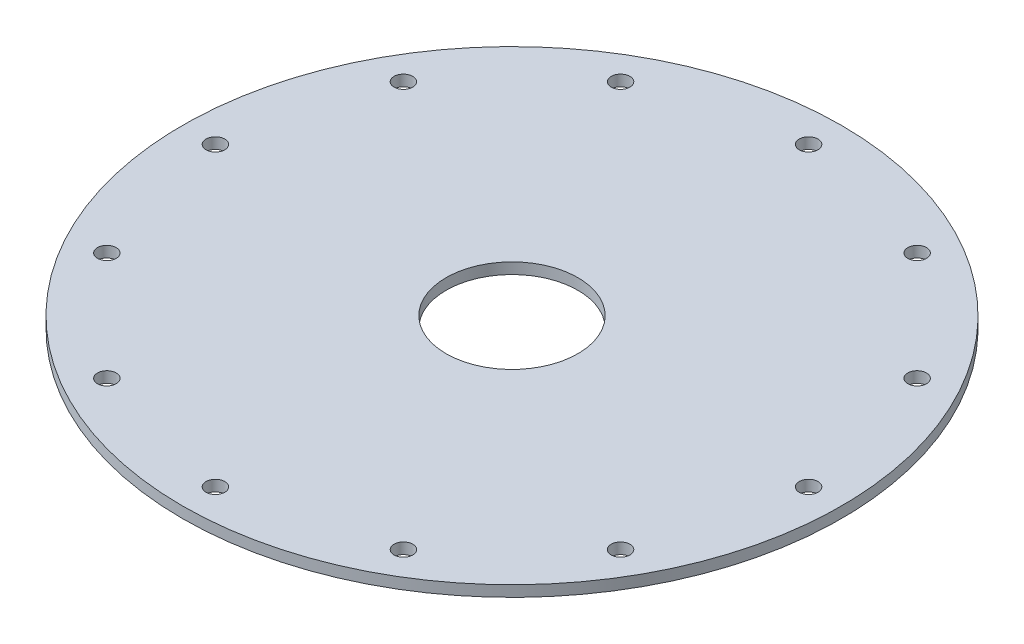
SolidWorks part; units mm, degrees
material "6063-T6"
ref_plane "Front Plane" through (0, 0, 0) normal (0, 0, 1) x (1, 0, 0)
ref_plane "Top Plane" through (0, 0, 0) normal (0, 1, 0) x (1, 0, 0)
ref_plane "Right Plane" through (0, 0, 0) normal (1, 0, 0) x (0, 0, -1)
ref_axis "Axis1" through (0, 55, 0) along (0, -1, 0)
sketch "Sketch1" plane through (0, 0, 0) normal (0, 0, 1) x (1, 0, 0)
  line L0 (-47.625, 0) -> (-9.525, 0)
  line L1 (0, 55) -> (0, -55) construction
  line L2 (-47.625, 0) -> (-47.625, 1.5875)
  line L3 (-47.625, 1.5875) -> (-9.525, 1.5875)
  line L4 (-47.625, 1.5875) -> (-9.525, 1.5875) construction
  line L5 (-9.525, 1.5875) -> (-9.525, 0)
  line L6 (-9.525, 0) -> (0, 0) construction
  line L7 (-47.625, 0) -> (-47.625, 1.5875) construction
  line L8 (-9.525, 1.5875) -> (-9.525, 0) construction
revolve "Revolve1" add sketch "Sketch1" angle 360 about axis through (0, 55, 0) along (0, -1, 0)
ref_plane "Hole Location Plane" through (0, 3.175, 0) normal (0, 1, 0) x (1, 0, 0)
sketch "Hole Location" plane through (0, 3.175, 0) normal (0, 1, 0) x (1, 0, 0)
  line L0 (0, 0) -> (-42.8625, 0) construction
  circle A0 centre (0, 0) radius 42.8625 construction
  dimension "D1" = 85.725
hole_wizard "#36 (0.1065) Diameter Hole1" positions "Sketch4" profile "Sketch5" hole size "#36" standard "ANSI Inch" end condition through all
sketch "Sketch4" plane through (0, 1.5875, 0) normal (0, 1, 0) x (1, 0, 0)
  point P0 (-42.8625, 0)
sketch "Sketch5" plane through (-42.8625, 1.5875, 0) normal (1, 0, 0) x (0, 0, 1)
  line L0 (0, 0) -> (0, 1.5875)
  line L1 (0, 1.5875) -> (1.3525, 1.5875)
  line L2 (1.3525, 1.5875) -> (1.3525, 0)
  line L5 (1.3525, 0) -> (0, 0)
  line L11 (0, -6.35) -> (0, 107.95) construction
  dimension "Thru Hole Dia." = 2.7051
  dimension "Thru Hole Depth" = 1.5875
pattern_circular "CirPattern1" count 12 every 30 about axis through (0, 0, 0) along (0, 1, 0) of "#36 (0.1065) Diameter Hole1"
equation "\"D1@Hole Location\"=\"TANK DIAMETER@Cryo Tank.Assembly\"+\"GASKET SEAT THICKNESS@Cryo Tank.Assembly\""
